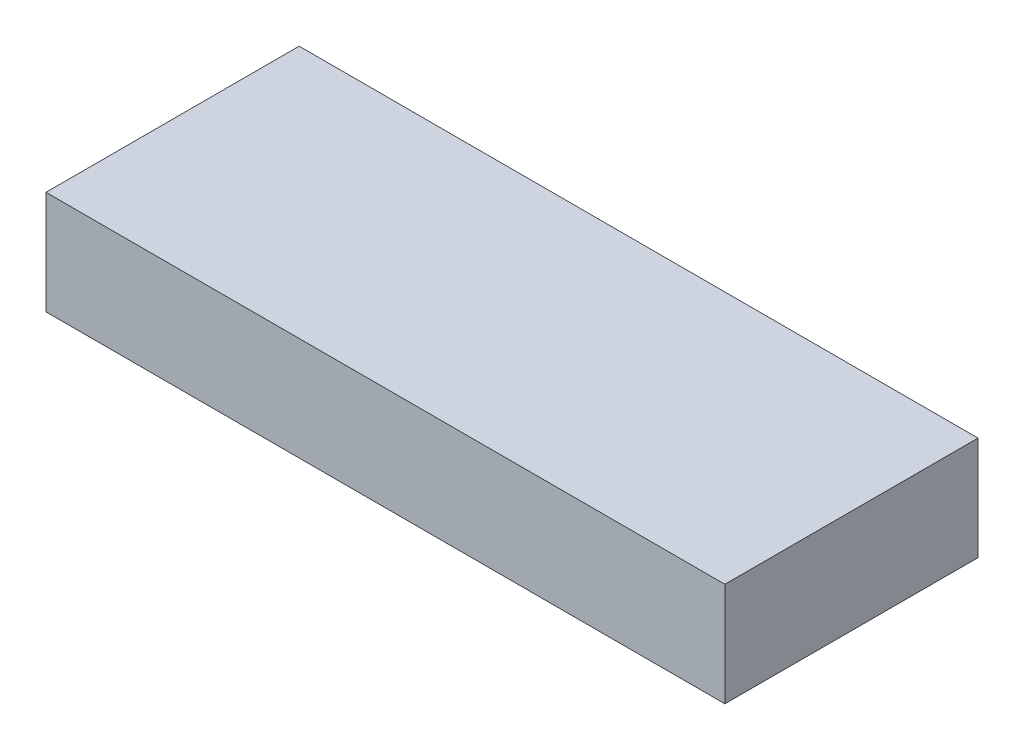
SolidWorks part; units mm, degrees
ref_plane "Front Plane" through (0, 0, 0) normal (0, 0, 1) x (1, 0, 0)
ref_plane "Top Plane" through (0, 0, 0) normal (0, 1, 0) x (1, 0, 0)
ref_plane "Right Plane" through (0, 0, 0) normal (1, 0, 0) x (0, 0, -1)
sketch "Sketch1" plane through (0, 0, 0) normal (0, 1, 0) x (1, 0, 0)
  line L1 (59, -22) -> (-59, -22)
  line L2 (59, -22) -> (59, 22)
  line L3 (59, 22) -> (-59, 22)
  line L4 (-59, -22) -> (-59, 22)
  line L5 (59, -22) -> (-59, 22) construction
  line L6 (59, 22) -> (-59, -22) construction
  point P0 (0, 0)
  dimension "D1" = 118
  dimension "D2" = 44
extrude "Extrude1" add sketch "Sketch1" along normal mid plane 18
sketch "Sketch3" plane through (0, 9, 0) normal (0, 1, 0) x (1, 0, 0)
  line L0 (-54, 22) -> (-54, -22)
  line L1 (59, 22) -> (-59, 22) construction
  line L2 (-59, -22) -> (59, -22) construction
  line L3 (-59, 22) -> (-59, -22) construction
  dimension "D1" = 5
sketch "Sketch4" plane through (0, 0, 22) normal (0, 0, 1) x (1, 0, 0)
  line L0 (-54, 9) -> (-54, -9)
  line L1 (-59, 9) -> (59, 9) construction
  line L2 (-59, -9) -> (59, -9) construction
  line L3 (-59, 9) -> (-59, -9) construction
  dimension "D1" = 5
sketch "Sketch5" plane through (0, -9, 0) normal (0, -1, 0) x (1, 0, 0)
  line L0 (-54, 22) -> (-54, -22)
sketch "Sketch6" plane through (0, 0, -22) normal (0, 0, -1) x (-1, 0, 0)
  line L0 (54, 9) -> (54, -9)
sketch "Sketch7" plane through (0, 9, 0) normal (0, 1, 0) x (1, 0, 0)
  line L0 (54, 22) -> (54, -22)
  line L1 (59, 22) -> (-59, 22) construction
  line L2 (-59, -22) -> (59, -22) construction
  line L3 (59, -22) -> (59, 22) construction
  dimension "D1" = 5
sketch "Sketch9" plane through (0, 0, 22) normal (0, 0, 1) x (1, 0, 0)
  line L0 (54, 9) -> (54, -9)
  line L1 (-59, 9) -> (59, 9) construction
  line L2 (-59, -9) -> (59, -9) construction
  line L3 (59, 9) -> (59, -9) construction
  dimension "D1" = 5
sketch "Sketch10" plane through (0, 0, -22) normal (0, 0, -1) x (-1, 0, 0)
  line L0 (-54, 9) -> (-54, -9)
sketch "Sketch11" plane through (0, -9, 0) normal (0, -1, 0) x (1, 0, 0)
  line L0 (-54, 22) -> (-54, -22)
  line L1 (54, 22) -> (54, -22)
sketch "Sketch16" plane through (0, 9, 0) normal (0, 1, 0) x (1, 0, 0)
  line L0 (-10, 22) -> (-10, -22)
  line L1 (59, 22) -> (-59, 22) construction
  line L2 (-59, -22) -> (59, -22) construction
  line L3 (-54, 22) -> (-54, -22) construction
  dimension "D1" = 44
sketch "Sketch17" plane through (0, 9, 0) normal (0, 1, 0) x (-1, 0, 0)
  line L0 (-10, -22) -> (-10, 22)
  line L1 (-59, -22) -> (59, -22) construction
  line L2 (59, 22) -> (-59, 22) construction
  line L4 (-54, -22) -> (-54, 22) construction
  line L5 (10, -22) -> (10, 22) construction
  dimension "D1" = 44
  dimension "D2" = 20
sketch "Sketch20" plane through (0, 0, -22) normal (0, 0, -1) x (-1, 0, 0)
  line L0 (-9.991, 9.0348) -> (-9.991, -4.0214)
  line L1 (9.8868, 9.0348) -> (9.8868, -4.0214)
sketch "Sketch21" plane through (0, 0, 22) normal (0, 0, 1) x (1, 0, 0)
  line L0 (-9.9981, 9) -> (-9.9981, -4.5497)
  line L1 (-59, 9) -> (59, 9) construction
  line L2 (9.8938, 9) -> (9.8938, -5.4379)
sketch "Sketch22" plane through (0, 0, -22) normal (0, 0, -1) x (-1, 0, 0)
  line L0 (-9.991, 0) -> (9.8868, 0)
  line L1 (-9.991, 9.0348) -> (-9.991, -4.0214) construction
  line L2 (9.8868, 9.0348) -> (9.8868, -4.0214) construction
sketch "Sketch23" plane through (0, 0, 22) normal (0, 0, 1) x (1, 0, 0)
  line L0 (-9.8868, 0) -> (9.991, 0)
